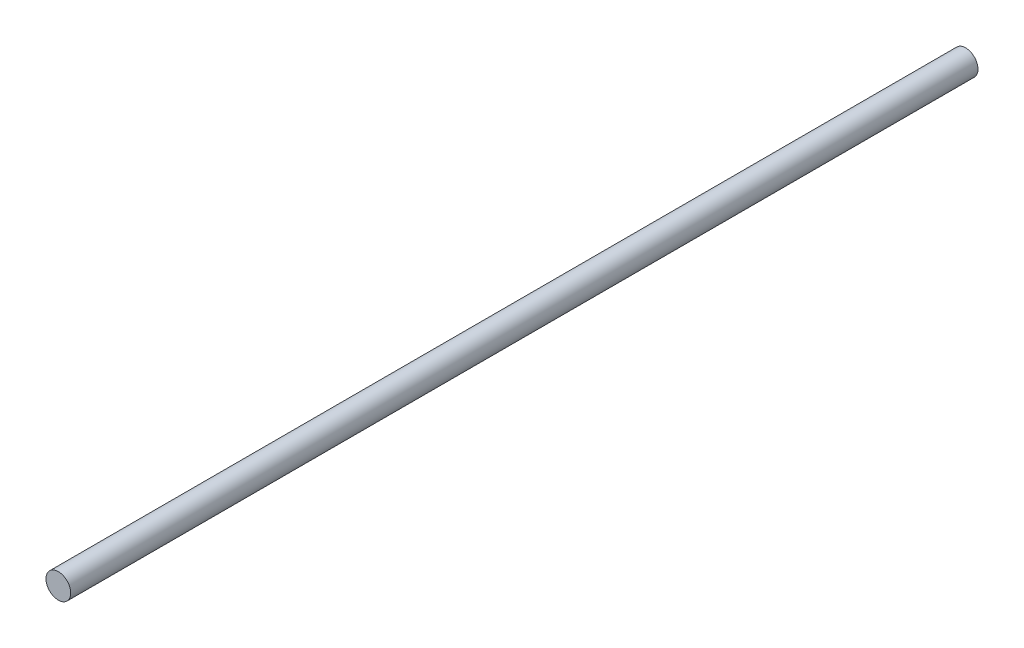
SolidWorks part; units mm, degrees
ref_plane "Front Plane" through (0, 0, 0) normal (0, 0, 1) x (1, 0, 0)
ref_plane "Top Plane" through (0, 0, 0) normal (0, 1, 0) x (1, 0, 0)
ref_plane "Right Plane" through (0, 0, 0) normal (1, 0, 0) x (0, 0, -1)
sketch "Sketch1" plane through (0, 0, 0) normal (0, 0, 1) x (1, 0, 0)
  circle A0 centre (0, 0) radius 3
  dimension "D1" = 6
extrude "Boss-Extrude1" add sketch "Sketch1" along normal blind 220
